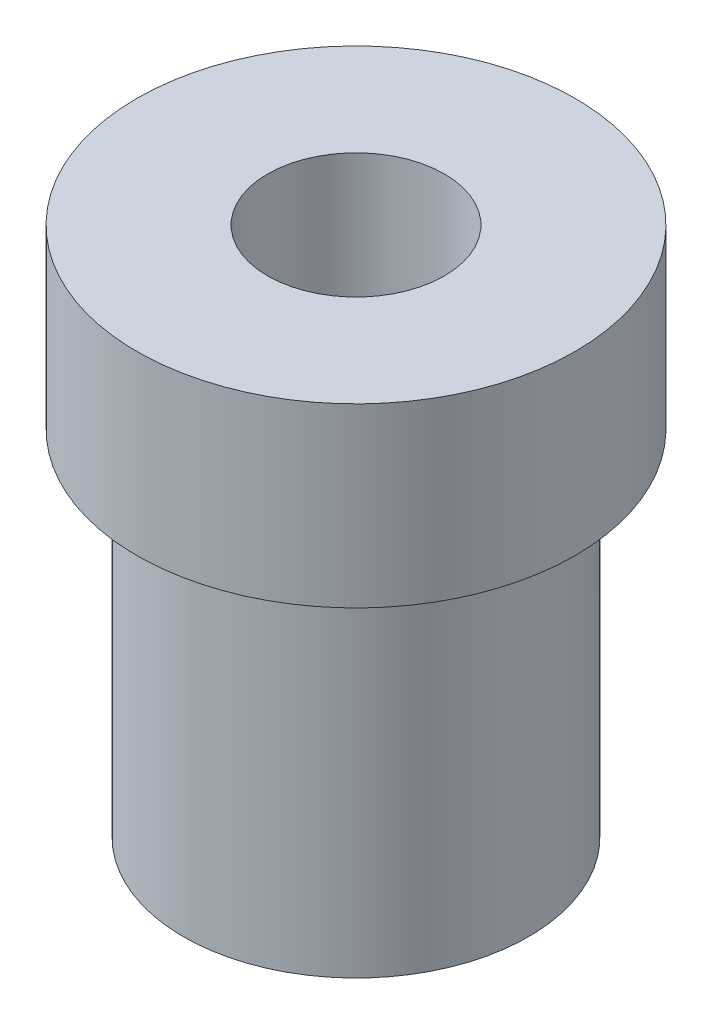
SolidWorks part; units mm, degrees
ref_plane "Front Plane" through (0, 0, 0) normal (0, 0, 1) x (1, 0, 0)
ref_plane "Top Plane" through (0, 0, 0) normal (0, 1, 0) x (1, 0, 0)
ref_plane "Right Plane" through (0, 0, 0) normal (1, 0, 0) x (0, 0, -1)
sketch "Sketch1" plane through (0, 0, 0) normal (0, 0, 1) x (1, 0, 0)
  line L0 (1.5875, 0) -> (1.5875, 9.525)
  line L1 (1.5875, 9.525) -> (3.937, 9.525)
  line L2 (3.937, 9.525) -> (3.937, 6.35)
  line L3 (3.937, 6.35) -> (3.0988, 6.35)
  line L4 (3.0988, 6.35) -> (3.0988, 0)
  line L5 (3.0988, 0) -> (1.5875, 0)
  line L6 (0, 0.1209) -> (0, -8357.9461) construction
  point P8 (0, 0)
  point P10 (4.1757, 7.725)
  dimension "D1" = 6.1976
  dimension "D2" = 3.175
  dimension "D3" = 6.35
  dimension "D4" = 7.874
  dimension "D5" = 3.175
revolve "Revolve1" add sketch "Sketch1" angle 360 about L6
